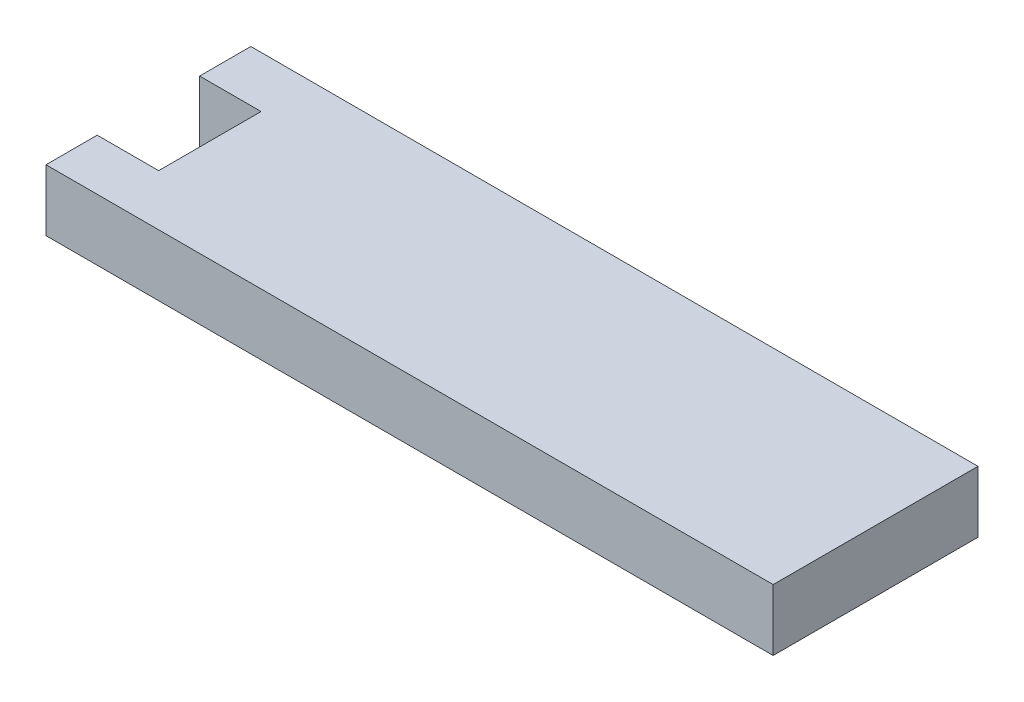
SolidWorks part; units mm, degrees
ref_plane "Front Plane" through (0, 0, 0) normal (0, 0, 1) x (1, 0, 0)
ref_plane "Top Plane" through (0, 0, 0) normal (0, 1, 0) x (1, 0, 0)
ref_plane "Right Plane" through (0, 0, 0) normal (1, 0, 0) x (0, 0, -1)
sketch "Sketch1" plane through (0, 0, 0) normal (0, 1, 0) x (1, 0, 0)
  line L1 (-35.5, 10) -> (35.5, 10)
  line L2 (-35.5, 10) -> (-35.5, -10)
  line L3 (-35.5, -10) -> (35.5, -10)
  line L4 (35.5, 10) -> (35.5, -10)
  line L5 (-35.5, 10) -> (35.5, -10) construction
  line L6 (-35.5, -10) -> (35.5, 10) construction
  point P0 (0, 0)
  dimension "D2" = 20
  dimension "D1" = 71
sketch "Sketch2" plane through (0, 0, 0) normal (0, 0, 1) x (1, 0, 0)
  line L0 (0, 0) -> (0, 6) construction
  line L1 (-35.5, 0) -> (35.5, 0) construction
  dimension "D1" = 6
extrude "Boss-Extrude1" add sketch "Sketch1" along normal up to vertex (6 mm away) contours L2 L3 L4 L1 up to point (0, 6, 0)
sketch "Sketch4" plane through (0, 0, 0) normal (0, -1, 0) x (1, 0, 0)
  line L11 (-35.5, -10) -> (-35.5, 10) construction
  line L14 (-35.5, 5) -> (-29.5, 5)
  line L15 (-35.5, 5) -> (-35.5, -5)
  line L17 (-35.5, -5) -> (-29.5, -5)
  line L19 (-29.5, 5) -> (-29.5, 10) construction
  line L20 (-35.5, 10) -> (35.5, 10) construction
  line L21 (-29.5, -5) -> (-29.5, -10) construction
  line L22 (-35.5, -10) -> (35.5, -10) construction
  line L23 (-29.5, 5) -> (-29.5, 0)
  line L24 (-29.5, 0) -> (-29.5, -5)
  point P6 (-68.2675, 5.7269)
  dimension "D1" = 6
extrude "Cut-Extrude1" cut sketch "Sketch4" against normal through all
equation "\"glass_width\" = 150"
equation "\"glass_height\"= 100"
equation "\"glass_thickness\"= 4"
equation "\"brood_space\"= 42"
equation "\"t1\"= 6"
equation "\"t2\"= 3.2"
equation "\"box_depth\"= \"brood_space\" + \"glass_thickness\" + \"glass_thickness\" + \"t2\" + \"t2\""
equation "\"box_width\"= \"glass_width\" + \"t1\" + \"t1\""
equation "\"food_height\"= 70"
equation "\"box_height\" = \"glass_height\" + ( \"t1\" * 3 ) + \"food_height\""
equation "\"D1@Sketch2\"=\"t1\""
equation "\"D1@Sketch4\"=\"t1\""
equation "\"D1@Sketch1\"= \"glass_height\" - 29"
